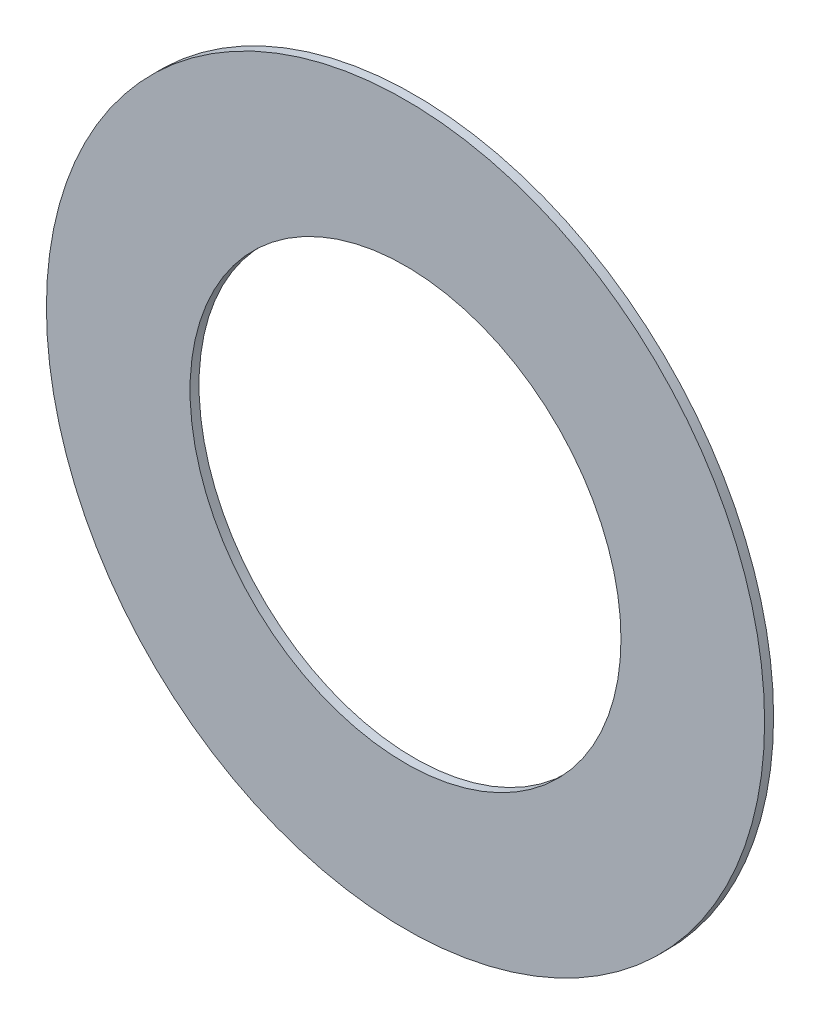
SolidWorks part; units mm, degrees
ref_plane "Front Plane" through (0, 0, 0) normal (0, 0, 1) x (1, 0, 0)
ref_plane "Top Plane" through (0, 0, 0) normal (0, 1, 0) x (1, 0, 0)
ref_plane "Right Plane" through (0, 0, 0) normal (1, 0, 0) x (0, 0, -1)
sketch "Sketch1" plane through (0, 0, 0) normal (0, 0, 1) x (1, 0, 0)
  circle A0 centre (0, 0) radius 127
  circle A1 centre (0, 0) radius 76.2
  dimension "D1" = 152.4
  dimension "D2" = 254
extrude "Boss-Extrude1" add sketch "Sketch1" along normal blind 3.175
